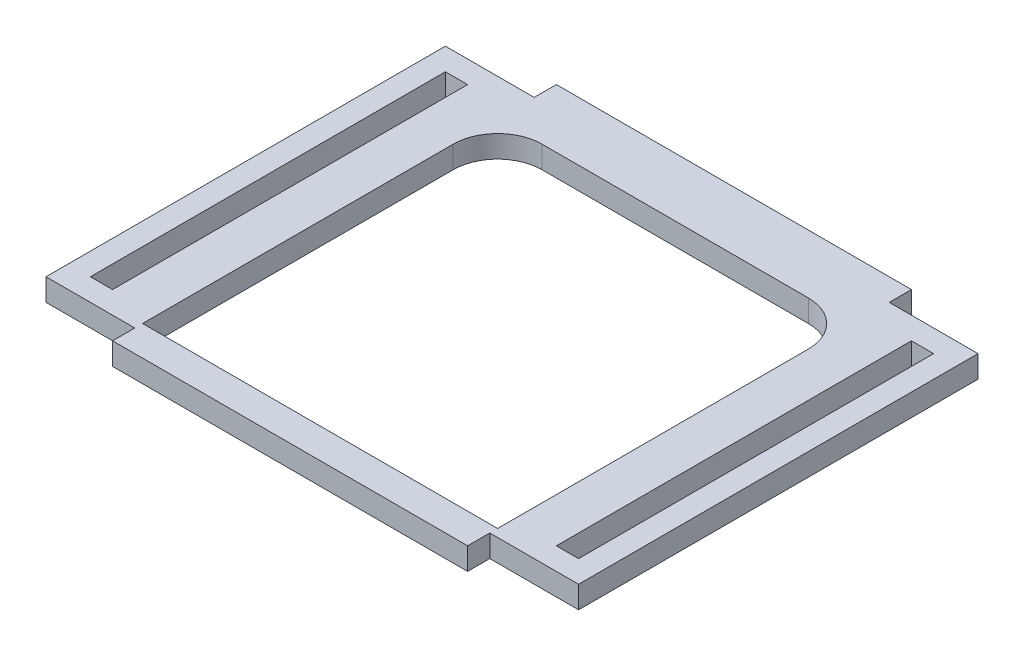
SolidWorks part; units mm, degrees
ref_plane "Front Plane" through (0, 0, 0) normal (0, 0, 1) x (1, 0, 0)
ref_plane "Top Plane" through (0, 0, 0) normal (0, 1, 0) x (1, 0, 0)
ref_plane "Right Plane" through (0, 0, 0) normal (1, 0, 0) x (0, 0, -1)
sketch "Sketch1" plane through (0, 0, 0) normal (0, 1, 0) x (1, 0, 0)
  line L1 (-76.2, -63.5) -> (76.2, -63.5)
  line L2 (-76.2, -63.5) -> (-76.2, 63.5)
  line L3 (-76.2, 63.5) -> (76.2, 63.5)
  line L4 (76.2, -63.5) -> (76.2, 63.5)
  line L5 (-76.2, -63.5) -> (76.2, 63.5) construction
  line L6 (-76.2, 63.5) -> (76.2, -63.5) construction
  point P0 (0, 0)
  dimension "D1" = 152.4
  dimension "D2" = 127
extrude "Boss-Extrude1" add sketch "Sketch1" along normal blind 6.35
sketch "Sketch2" plane through (0, 0, 0) normal (0, 1, 0) x (1, 0, 0)
  line L0 (0, 63.5) -> (0, -63.5) construction
  line L1 (76.2, 63.5) -> (-76.2, 63.5) construction
  line L2 (-76.2, -63.5) -> (76.2, -63.5) construction
  line L3 (0, 0) -> (-76.2, 0) construction
  line L4 (-76.2, 63.5) -> (-76.2, -63.5) construction
  line L5 (0, 0) -> (76.2, 0) construction
  line L6 (76.2, -63.5) -> (76.2, 63.5) construction
  line L7 (-76.2, 63.5) -> (-76.2, 57.15)
  line L8 (-76.2, -63.5) -> (-50.8, -63.5)
  line L9 (-76.2, -63.5) -> (-76.2, -57.15)
  line L10 (-76.2, -57.15) -> (-50.8, -57.15)
  line L11 (-50.8, -63.5) -> (-50.8, -57.15)
  line L12 (-76.2, 63.5) -> (-50.8, 63.5)
  line L13 (-50.8, 63.5) -> (-50.8, 57.15)
  line L14 (-76.2, 57.15) -> (-50.8, 57.15)
  line L15 (50.8, -63.5) -> (50.8, -57.15)
  line L16 (76.2, -63.5) -> (50.8, -63.5)
  line L17 (76.2, -63.5) -> (76.2, -57.15)
  line L18 (76.2, -57.15) -> (50.8, -57.15)
  line L19 (76.2, 63.5) -> (76.2, 57.15)
  line L20 (76.2, 63.5) -> (50.8, 63.5)
  line L21 (50.8, 63.5) -> (50.8, 57.15)
  line L22 (76.2, 57.15) -> (50.8, 57.15)
  line L23 (69.85, -50.8) -> (63.5, -50.8)
  line L24 (-69.85, 50.8) -> (-63.5, 50.8)
  line L25 (-69.85, 50.8) -> (-69.85, -50.8)
  line L26 (-69.85, -50.8) -> (-63.5, -50.8)
  line L27 (-63.5, 50.8) -> (-63.5, -50.8)
  line L28 (69.85, 50.8) -> (69.85, -50.8)
  line L29 (63.5, 50.8) -> (63.5, -50.8)
  line L30 (69.85, 50.8) -> (63.5, 50.8)
  point P35 (-66.675, -50.8)
  dimension "D1" = 6.35
  dimension "D2" = 25.4
  dimension "D3" = 6.35
  dimension "D4" = 12.7
  dimension "D5" = 12.7
  dimension "D6" = 6.35
extrude "Cut-Extrude1" cut sketch "Sketch2" against normal blind 6.35 and the other way through all contours L7 L14 L13 L12 | L25 L24 L27 L26 | L9 L8 L11 L10 | L23 L29 L30 L28 | L19 L22 L21 L20 | L15 L18 L17 L16
sketch "Sketch3" plane through (0, 0, 0) normal (0, 1, 0) x (1, 0, 0)
  line L0 (50.8, 63.5) -> (-50.8, 63.5) construction
  line L1 (-50.8, -54.9142) -> (50.8, -54.9142)
  line L2 (-50.8, -54.9142) -> (-50.8, 33.9858)
  line L3 (-38.1, 46.6858) -> (38.1, 46.6858)
  line L4 (50.8, -54.9142) -> (50.8, 33.9858)
  line L5 (76.2, -57.15) -> (76.2, 57.15) construction
  arc A0 (38.1, 46.6858) -> (50.8, 33.9858) centre (38.1, 33.9858) cw
  arc A1 (-50.8, 33.9858) -> (-38.1, 46.6858) centre (-38.1, 33.9858) cw
  point P12 (-50.8, 46.6858)
  dimension "D5" = 12.7
  dimension "D1" = 101.6
  dimension "D2" = 101.6
  dimension "D3" = 16.8142
  dimension "D4" = 25.4
extrude "Cut-Extrude2" cut sketch "Sketch3" against normal blind 127 and the other way blind 127
